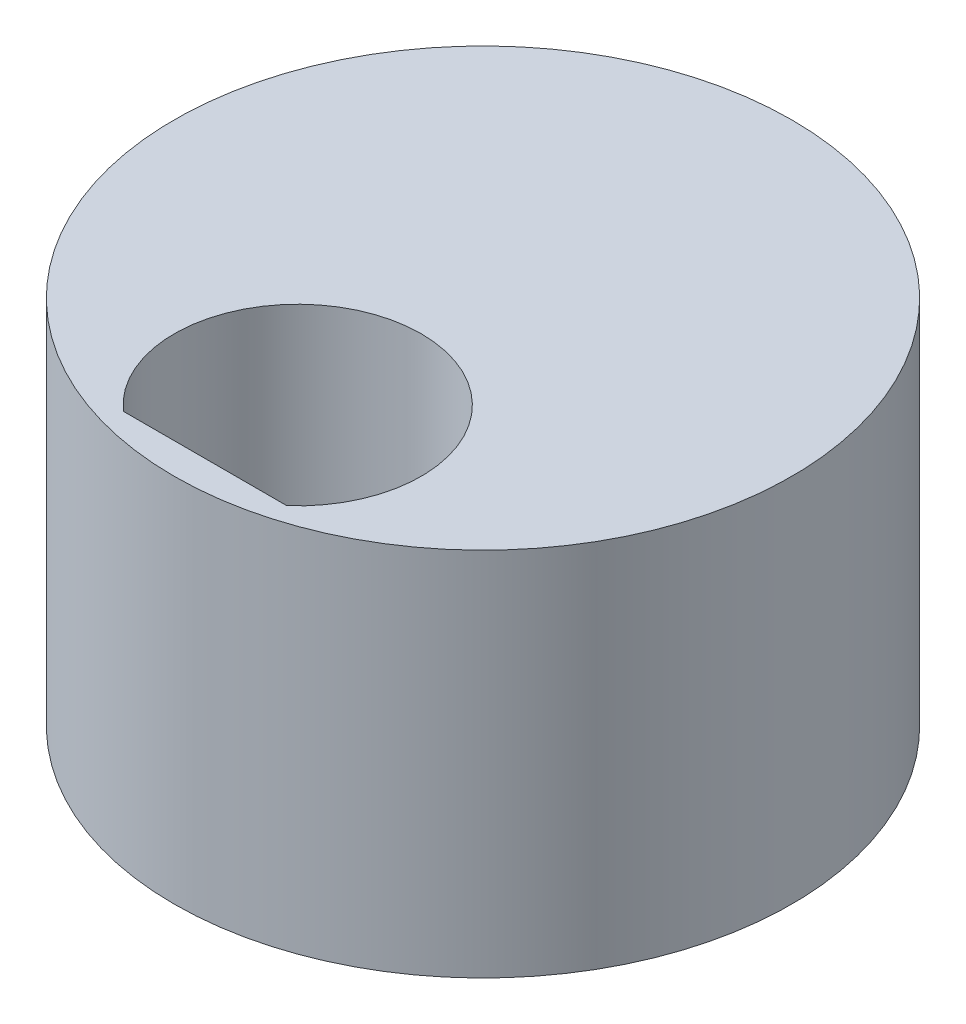
SolidWorks part; units mm, degrees
ref_plane "Front Plane" through (0, 0, 0) normal (0, 0, 1) x (1, 0, 0)
ref_plane "Top Plane" through (0, 0, 0) normal (0, 1, 0) x (1, 0, 0)
ref_plane "Right Plane" through (0, 0, 0) normal (1, 0, 0) x (0, 0, -1)
sketch "Sketch1" plane through (0, 0, 0) normal (0, 1, 0) x (1, 0, 0)
  line L0 (1.3229, -4.5) -> (-1.3229, -4.5)
  circle A0 centre (0, 0) radius 5
  arc A1 (1.3229, -4.5) -> (-1.3229, -4.5) centre (0, -3) ccw
  dimension "3" = 3
extrude "Boss-Extrude1" add sketch "Sketch1" along normal blind 6
